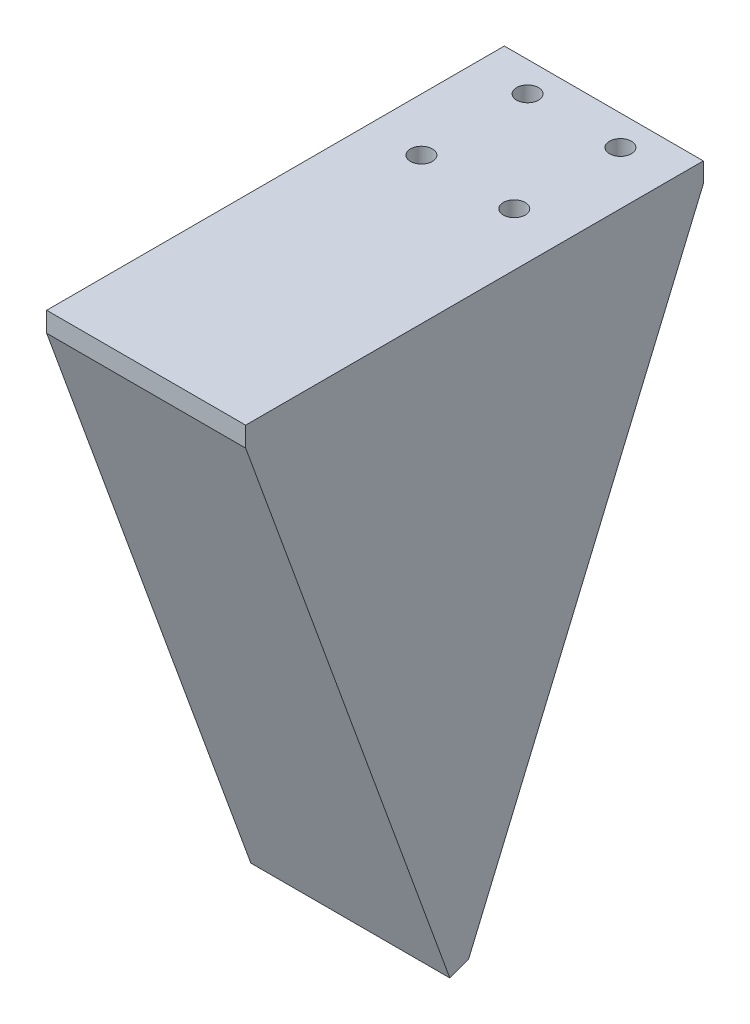
SolidWorks part; units mm, degrees
ref_plane "Front Plane" through (0, 0, 0) normal (0, 0, 1) x (1, 0, 0)
ref_plane "Top Plane" through (0, 0, 0) normal (0, 1, 0) x (1, 0, 0)
ref_plane "Right Plane" through (0, 0, 0) normal (1, 0, 0) x (0, 0, -1)
sketch "Sketch1" plane through (0, 0, 0) normal (0, 1, 0) x (1, 0, 0)
  line L2 (15, -28) -> (15, 30)
  line L3 (15, 30) -> (-15, 30)
  line L4 (-15, -28) -> (-15, 30)
  line L6 (-15, -28) -> (-15, -31)
  line L8 (-15, -31) -> (15, -31)
  line L9 (15, -28) -> (15, -31)
  point P0 (0, 0)
extrude "Boss-Extrude1" add sketch "Sketch1" along normal blind 3
sketch "Sketch2" plane through (0, 3, 0) normal (0, 1, 0) x (1, 0, 0)
  circle A1 centre (-7, 25.5) radius 1.65
  circle A2 centre (7, 25.5) radius 1.65
  circle A3 centre (-7, 9.5) radius 1.65
  circle A4 centre (7, 9.5) radius 1.65
extrude "Cut-Extrude1" cut sketch "Sketch2" against normal blind 4
sketch "Sketch3" plane through (0, 0, 31) normal (0, 0, 1) x (1, 0, 0)
  line L4 (-15, 0) -> (15, 0)
  line L5 (15, 0) -> (15, 3)
  line L6 (15, 3) -> (-15, 3)
  line L7 (-15, 3) -> (-15, 0)
  line L8 (-15, 0) -> (15, 0)
  line L9 (15, 0) -> (15, 3)
  line L10 (15, 3) -> (-15, 3)
  line L11 (-15, 3) -> (-15, 0)
  dimension "D1" = 0
extrude "Boss-Extrude2" add sketch "Sketch3" along normal blind 8
sketch "Sketch5" plane through (-15, 0, 0) normal (-1, 0, 0) x (0, 0, 1)
  line L0 (39, 0) -> (8.2182, -84.5723)
  line L1 (-30, 0) -> (39, 0) construction
  line L2 (8.2182, -84.5723) -> (5.3991, -83.5463)
  line L3 (5.3991, -83.5463) -> (35.8075, 0)
  line L4 (35.8075, 0) -> (39, 0)
  dimension "D1" = 70
extrude "Boss-Extrude3" add sketch "Sketch5" against normal up to surface (30 mm away) up to face at (15, 1.5, 4.5)
sketch "Sketch6" plane through (15, 0, 0) normal (1, 0, 0) x (0, 0, -1)
  line L0 (30, 0) -> (-5.3991, -83.5463)
  line L7 (-39, 3) -> (-39, 0)
  line L8 (-39, 0) -> (-8.2182, -84.5723)
  line L9 (-8.2182, -84.5723) -> (-5.3991, -83.5463)
  line L10 (-5.3991, -83.5463) -> (-35.8075, 0)
  line L11 (-35.8075, 0) -> (30, 0)
  line L12 (30, 0) -> (30, 3)
  line L13 (30, 3) -> (-39, 3)
  line L14 (-39, 3) -> (-39, 0)
  line L15 (-39, 0) -> (-8.2182, -84.5723)
  line L16 (-8.2182, -84.5723) -> (-5.3991, -83.5463)
  line L19 (30, 0) -> (30, 3)
  line L20 (30, 3) -> (-39, 3)
  dimension "D1" = 0
extrude "Boss-Extrude4" add sketch "Sketch6" against normal blind 3
